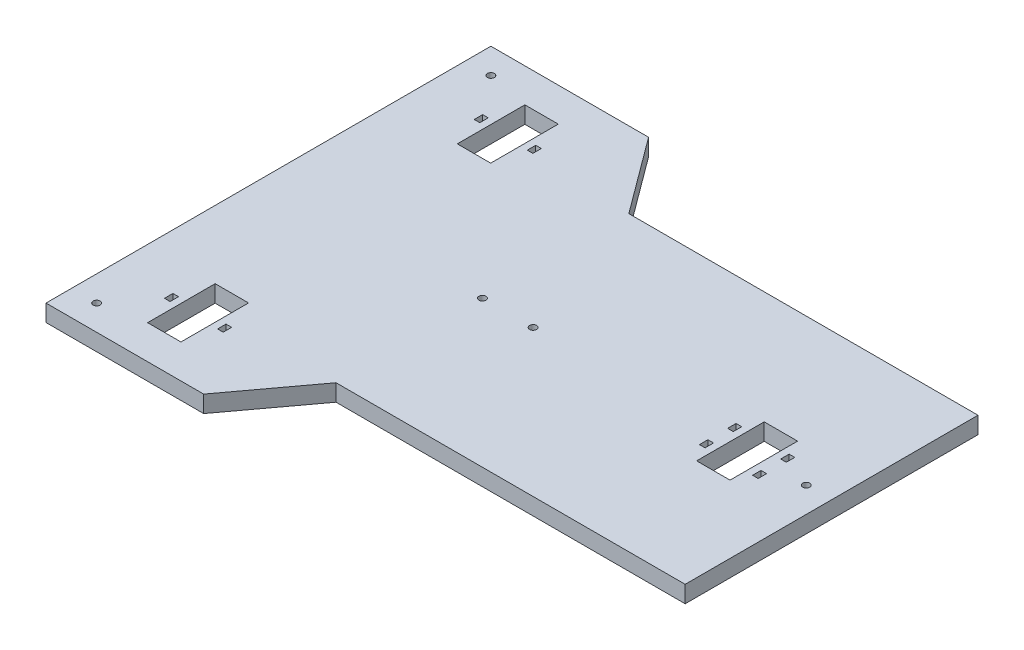
SolidWorks part; units mm, degrees
ref_plane "Plan de face" through (0, 0, 0) normal (0, 0, 1) x (1, 0, 0)
ref_plane "Plan de dessus" through (0, 0, 0) normal (0, 1, 0) x (1, 0, 0)
ref_plane "Plan de droite" through (0, 0, 0) normal (1, 0, 0) x (0, 0, -1)
sketch "Esquisse1" plane through (0, 0, 0) normal (0, 1, 0) x (1, 0, 0)
  line L0 (200.6543, 26.8836) -> (200.6543, 130.8836)
  line L1 (200.6543, 130.8836) -> (76.6546, 130.8836)
  line L2 (76.6546, 130.8836) -> (56.6546, 157.8836)
  line L3 (56.6546, 157.8836) -> (0.6543, 157.8836)
  line L4 (0.6543, 157.8836) -> (0.6543, -0.1164)
  line L5 (200.6543, 78.8836) -> (0.6543, 78.8836) construction
  line L6 (30.6544, 121.8836) -> (30.6544, 35.8836) construction
  line L7 (170.6544, 90.8836) -> (170.6544, 66.8836) construction
  line L8 (0.6543, -0.1164) -> (56.6546, -0.1164)
  line L9 (56.6546, -0.1164) -> (76.6546, 26.8836)
  line L10 (76.6546, 26.8836) -> (200.6543, 26.8836)
  line L14 (22.2256, 135.3836) -> (22.2256, 132.3836)
  line L15 (22.2256, 132.3836) -> (20.2256, 132.3836)
  line L16 (20.2256, 132.3836) -> (20.2256, 135.3836)
  line L17 (20.2256, 135.3836) -> (22.2256, 135.3836)
  line L18 (39.0832, 132.3836) -> (39.0832, 135.3836)
  line L19 (39.0832, 135.3836) -> (41.0832, 135.3836)
  line L20 (41.0832, 135.3836) -> (41.0832, 132.3836)
  line L21 (41.0832, 132.3836) -> (39.0832, 132.3836)
  line L22 (20.2256, 25.3836) -> (22.2256, 25.3836)
  line L23 (22.2256, 25.3836) -> (22.2256, 22.3836)
  line L24 (22.2256, 22.3836) -> (20.2256, 22.3836)
  line L25 (20.2256, 22.3836) -> (20.2256, 25.3836)
  line L26 (41.0832, 25.3836) -> (41.0832, 22.3836)
  line L27 (41.0832, 22.3836) -> (39.0832, 22.3836)
  line L28 (39.0832, 22.3836) -> (39.0832, 25.3836)
  line L29 (39.0832, 25.3836) -> (41.0832, 25.3836)
  line L30 (162.2256, 72.3836) -> (160.2256, 72.3836)
  line L31 (160.2256, 72.3836) -> (160.2256, 75.3836)
  line L32 (160.2256, 75.3836) -> (162.2256, 75.3836)
  line L33 (162.2256, 75.3836) -> (162.2256, 72.3836)
  line L34 (181.0832, 85.3836) -> (181.0832, 82.3836)
  line L35 (181.0832, 82.3836) -> (179.0832, 82.3836)
  line L36 (179.0832, 82.3836) -> (179.0832, 85.3836)
  line L37 (179.0832, 85.3836) -> (181.0832, 85.3836)
  line L38 (36.5832, 145.8836) -> (36.5832, 121.8836)
  line L39 (36.5832, 121.8836) -> (24.7256, 121.8836)
  line L40 (24.7256, 121.8836) -> (24.7256, 145.8836)
  line L41 (24.7256, 145.8836) -> (36.5832, 145.8836)
  line L42 (24.7256, 11.8836) -> (24.7256, 35.8836)
  line L43 (24.7256, 35.8836) -> (36.5832, 35.8836)
  line L44 (36.5832, 35.8836) -> (36.5832, 11.8836)
  line L45 (36.5832, 11.8836) -> (24.7256, 11.8836)
  line L46 (176.5832, 90.8836) -> (176.5832, 66.8836)
  line L47 (176.5832, 66.8836) -> (164.7256, 66.8836)
  line L48 (164.7256, 66.8836) -> (164.7256, 90.8836)
  line L49 (164.7256, 90.8836) -> (176.5832, 90.8836)
  line L170 (179.0832, 72.3836) -> (179.0832, 75.3836)
  line L171 (179.0832, 75.3836) -> (181.0832, 75.3836)
  line L172 (181.0832, 75.3836) -> (181.0832, 72.3836)
  line L173 (181.0832, 72.3836) -> (179.0832, 72.3836)
  line L174 (162.2256, 85.3836) -> (162.2256, 82.3836)
  line L175 (162.2256, 82.3836) -> (160.2256, 82.3836)
  line L176 (160.2256, 82.3836) -> (160.2256, 85.3836)
  line L177 (160.2256, 85.3836) -> (162.2256, 85.3836)
  dimension "D2" = 158
  dimension "D3" = 56.0002
  dimension "D4" = 200
  dimension "D5" = 104
  dimension "D6" = 12
  dimension "D7" = 11.8577
  dimension "D8" = 140
  dimension "D9" = 3.5
  dimension "D10" = 24
  dimension "D11" = 3.5
  dimension "D12" = 12
  dimension "D13" = 24.0713
  dimension "D14" = 123.9998
  dimension "D15" = 3
  dimension "D16" = 2
  dimension "D17" = 2.5
  dimension "D18" = 2.5
  dimension "D19" = 2.5
  dimension "D20" = 2.5
extrude "Boss.-Extru.1" add sketch "Esquisse1" along normal blind 6
hole_wizard "Dégagement M2.51" positions "Esquisse3" profile "Esquisse4" hole size "M2.5" standard "Din" end condition through all
sketch "Esquisse3" plane through (0, 6, 0) normal (0, 1, 0) x (1, 0, 0)
  line L0 (0.6543, -0.1164) -> (56.6546, -0.1164) construction
  line L1 (0.6543, 157.8836) -> (0.6543, -0.1164) construction
  line L2 (56.6546, 157.8836) -> (0.6543, 157.8836) construction
  line L3 (200.6543, 26.8836) -> (200.6543, 130.8836) construction
  line L4 (200.6543, 78.8836) -> (0.6543, 78.8836) construction
  point P0 (9.6543, 148.8836)
  point P2 (9.6543, 8.8836)
  point P4 (76.6543, 78.8836)
  point P6 (94.6543, 78.8836)
  point P8 (191.6543, 78.8836)
  dimension "D1" = 9
  dimension "D2" = 9
  dimension "D3" = 9
  dimension "D4" = 9
  dimension "D5" = 9
  dimension "D6" = 76
  dimension "D7" = 106
  dimension "D8" = 140
  dimension "D9" = 182
  dimension "D10" = 18
sketch "Esquisse4" plane through (9.6543, 6, -148.8836) normal (1, 0, 0) x (0, 0, 1)
  line L0 (0, 0) -> (0, 6)
  line L1 (0, 6) -> (1.25, 6)
  line L2 (1.25, 6) -> (1.25, 0)
  line L5 (1.25, 0) -> (0, 0)
  line L11 (0, -6.35) -> (0, 107.95) construction
  dimension "Diamètre du perçage jusqu'au prochain" = 2.5
  dimension "Profondeur du perçage jusqu'au prochain" = 6
ref_plane "Plan1" through (0, 0, -78.8836) normal (0, 0, 1) x (1, 0, 0)
ref_plane "Plan2" through (100, 0, 0) normal (1, 0, 0) x (0, 0, -1)
hole_wizard "Dégagement M31" positions "Esquisse6" profile "Esquisse5" hole size "M3" standard "Din"
sketch "Esquisse6" plane through (0, 0, 0) normal (0, -1, 0) x (-1, 0, 0)
  point P0 (-191.6543, 78.8836)
  point P3 (-9.6543, 8.8836)
  point P6 (-9.6543, 148.8836)
sketch "Esquisse5" plane through (191.6543, 0, -78.8836) normal (1, 0, 0) x (0, 0, -1)
  line L0 (0, 0) -> (0, 4)
  line L1 (0, 4) -> (1.625, 4)
  line L2 (1.625, 4) -> (1.625, 0)
  line L5 (1.625, 0) -> (0, 0)
  line L10 (0, 4) -> (-1.625, 4) construction
  line L11 (0, -6.35) -> (0, 107.95) construction
  dimension "Diamètre du perçage" = 3.25
  dimension "Profondeur du perçage" = 4
  dimension "Angle de pointe" = 180
